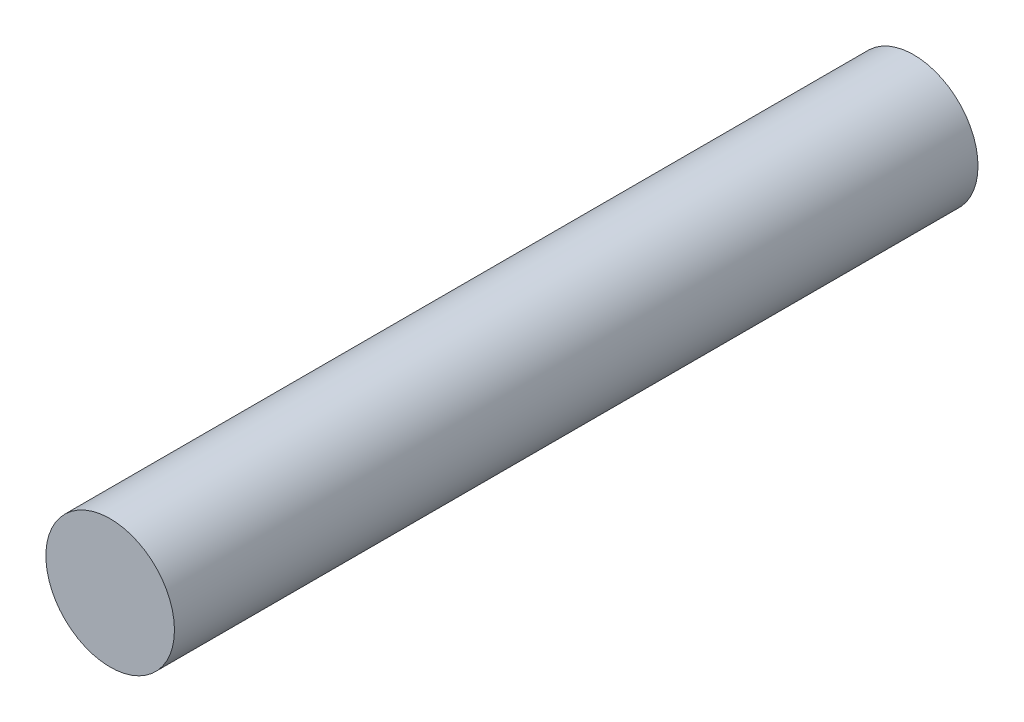
SolidWorks part; units mm, degrees
ref_plane "Front Plane" through (0, 0, 0) normal (0, 0, 1) x (1, 0, 0)
ref_plane "Top Plane" through (0, 0, 0) normal (0, 1, 0) x (1, 0, 0)
ref_plane "Right Plane" through (0, 0, 0) normal (1, 0, 0) x (0, 0, -1)
sketch "Sketch1" plane through (0, 0, 0) normal (0, 0, 1) x (1, 0, 0)
  circle A0 centre (0, 0) radius 4
  dimension "D1" = 8
extrude "Boss-Extrude1" add sketch "Sketch1" along normal blind 50
